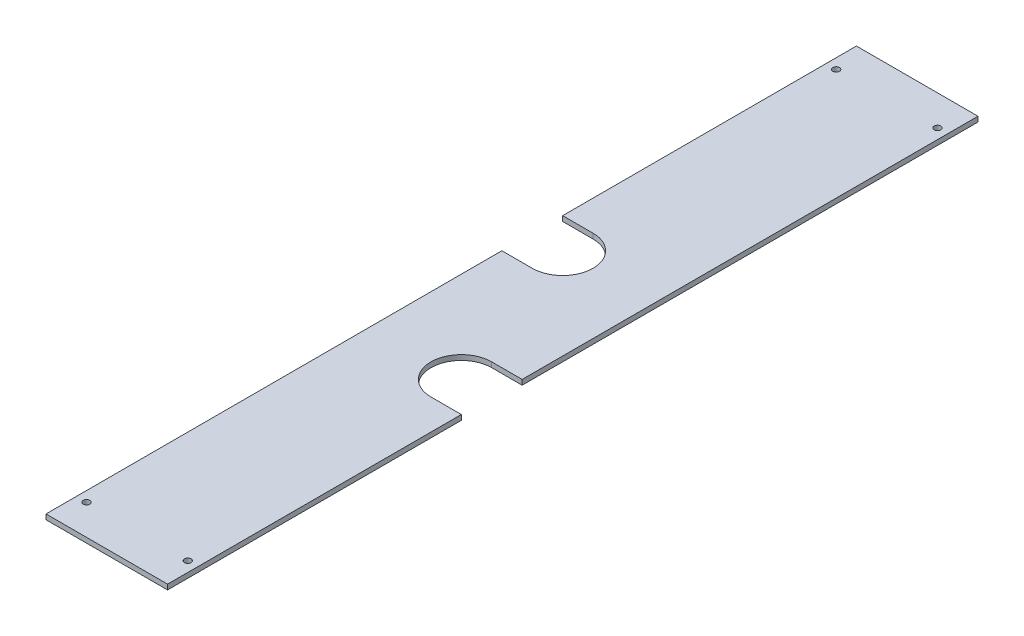
SolidWorks part; units mm, degrees
ref_plane "Front Plane" through (0, 0, 0) normal (0, 0, 1) x (1, 0, 0)
ref_plane "Top Plane" through (0, 0, 0) normal (0, 1, 0) x (1, 0, 0)
ref_plane "Right Plane" through (0, 0, 0) normal (1, 0, 0) x (0, 0, -1)
sketch "Sketch1" plane through (0, 0, 0) normal (0, 0, 1) x (1, 0, 0)
  line L0 (-38.0447, -22.987) -> (38.0447, -22.987) construction
  line L1 (-38.1, -16.637) -> (38.1, -16.637) construction
  line L2 (-38.1, -16.637) -> (-38.1, -13.462) construction
  line L3 (-38.1, -13.462) -> (38.1, -13.462) construction
  line L4 (38.1, -16.637) -> (38.1, -13.462) construction
  line L5 (-38.1, 22.8953) -> (38.1, 22.8953)
  line L6 (-38.1, 22.8953) -> (-38.1, 19.7203)
  line L7 (-38.1, 19.7203) -> (38.1, 19.7203)
  line L8 (38.1, 22.8953) -> (38.1, 19.7203)
  line L9 (-39.7905, -19.812) -> (39.7905, -19.812) construction
  circle A0 centre (0, 0) radius 44.45 construction
  circle A1 centre (0, 0) radius 47.625 construction
  point P12 (0, -47.625)
  dimension "D1" = 88.9
  dimension "D5" = 95.25
  dimension "D2" = 3.175
  dimension "D3" = 3.175
  dimension "D4" = 76.2
  dimension "D6" = 24.638
  dimension "D7" = 3.175
  dimension "D8" = 3.175
extrude "Boss-Extrude1" add sketch "Sketch1" along normal blind 508 contours L3 L4 L1 L2 | L7 L8 L5 L6
sketch "Sketch2" plane through (0, 22.8953, 0) normal (0, 1, 0) x (1, 0, 0)
  line L0 (-38.1, -508) -> (38.1, -508) construction
  line L1 (-38.1, -508) -> (-38.1, 0) construction
  line L2 (-19.05, -184.15) -> (-38.1, -184.15)
  line L3 (-38.1, -184.15) -> (-38.1, -222.25)
  line L4 (-38.1, -222.25) -> (-19.05, -222.25)
  line L5 (38.1, -508) -> (38.1, 0) construction
  line L6 (19.05, -323.85) -> (38.1, -323.85)
  line L7 (38.1, -323.85) -> (38.1, -285.75)
  line L8 (38.1, -285.75) -> (19.05, -285.75)
  line L9 (-38.1, 0) -> (38.1, 0) construction
  arc A0 (-19.05, -222.25) -> (-19.05, -184.15) centre (-19.05, -203.2) ccw
  arc A1 (19.05, -285.75) -> (19.05, -323.85) centre (19.05, -304.8) ccw
  dimension "D1" = 304.8
  dimension "D2" = 38.1
  dimension "D4" = 38.1
  dimension "D3" = 19.05
  dimension "D5" = 19.05
  dimension "D6" = 304.8
extrude "Cut-Extrude1" cut sketch "Sketch2" against normal through all
ref_plane "Plane1" through (0, 0, 254) normal (0, 0, 1) x (1, 0, 0)
sketch "Sketch4" plane through (0, 22.8953, 0) normal (0, 1, 0) x (1, 0, 0)
  line L0 (-38.1, -508) -> (38.1, -508) construction
  line L1 (-38.1, -508) -> (-38.1, -222.25) construction
  line L2 (-38.1, 0) -> (38.1, 0) construction
  line L3 (38.1, -285.75) -> (38.1, 0) construction
  circle A0 centre (-31.75, -488.95) radius 2.0828
  circle A1 centre (31.75, -19.05) radius 2.0828
  dimension "D1" = 19.05
  dimension "D2" = 4.1656
  dimension "D4" = 4.1656
  dimension "D3" = 6.35
  dimension "D5" = 19.05
  dimension "D6" = 6.35
extrude "Cut-Extrude2" cut sketch "Sketch4" against normal through all
mirror "Mirror2" about plane through (0, 0, 254) normal (0, 0, 1) of "Cut-Extrude2"
